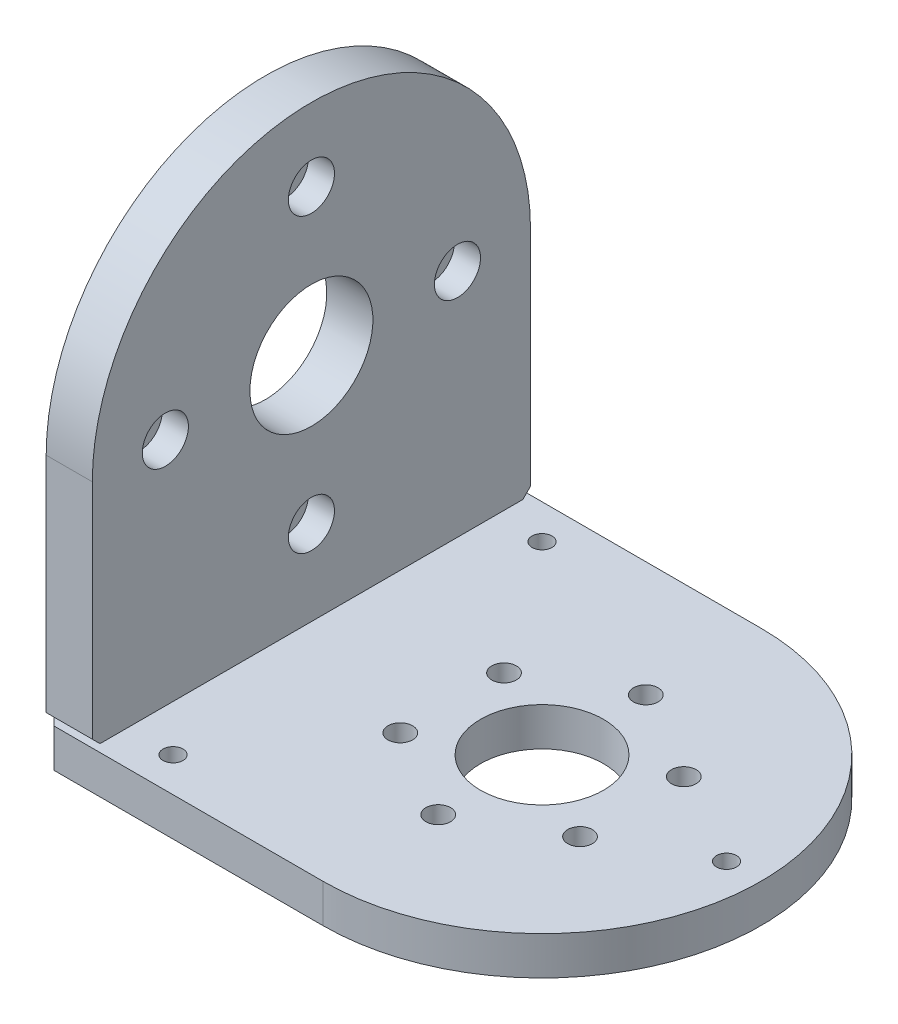
SolidWorks part; units mm, degrees
material "5052-H32"
ref_plane "前视基准面" through (0, 0, 0) normal (0, 0, 1) x (1, 0, 0)
ref_plane "上视基准面" through (0, 0, 0) normal (0, 1, 0) x (1, 0, 0)
ref_plane "右视基准面" through (0, 0, 0) normal (1, 0, 0) x (0, 0, -1)
other "Configuration Table"
sketch "草图1" plane through (0, 0, 0) normal (0, 1, 0) x (1, 0, 0)
  line L1 (-33, 28.5) -> (33, 28.5)
  line L2 (-33, 28.5) -> (-33, -28.5)
  line L3 (-33, -28.5) -> (33, -28.5)
  line L4 (33, 28.5) -> (33, -28.5)
  line L5 (-33, 28.5) -> (33, -28.5) construction
  line L6 (-33, -28.5) -> (33, 28.5) construction
  point P0 (0, 0)
  dimension "D1" = 66
  dimension "D2" = 57
extrude "凸台-拉伸1" add sketch "草图1" along normal blind 5
sketch "草图12" plane through (-33, 0, 0) normal (-1, 0, 0) x (0, 0, 1)
  line L0 (28.5, 5) -> (28.5, 0) construction
  line L1 (-28.5, 5) -> (28.5, 5)
  line L2 (-28.5, 5) -> (-28.5, 65)
  line L3 (-28.5, 65) -> (28.5, 65)
  line L4 (28.5, 5) -> (28.5, 65)
  dimension "D1" = 60
extrude "凸台-拉伸2" add sketch "草图12" against normal blind 6 separate body
sketch "草图13" plane through (0, 5, 0) normal (0, 1, 0) x (1, 0, 0)
  line L0 (33, -28.5) -> (33, 28.5) construction
  line L1 (33, 28.5) -> (-33, 28.5) construction
  line L2 (-33, -28.5) -> (33, -28.5) construction
  line L3 (3, -28.5) -> (33, -28.5)
  line L4 (33, -28.5) -> (33, 28.5)
  line L5 (33, 28.5) -> (3, 28.5)
  circle A0 centre (3, 0) radius 8
  arc A1 (3, -28.5) -> (3, 28.5) centre (3, 0) ccw
  dimension "D1" = 30
  dimension "D2" = 16
extrude "切除-拉伸2" cut sketch "草图13" against normal blind 6
sketch "草图14" plane through (-33, 0, 0) normal (-1, 0, 0) x (0, 0, 1)
  line L0 (28.5, 65) -> (-28.5, 65) construction
  circle A0 centre (0, 35) radius 8
  dimension "D1" = 16
  dimension "D2" = 30
extrude "切除-拉伸3" cut sketch "草图14" against normal blind 6
sketch "草图15" plane through (-33, 0, 0) normal (-1, 0, 0) x (0, 0, 1)
  line L0 (28.5, 5) -> (28.5, 65) construction
  line L1 (28.5, 65) -> (-28.5, 65) construction
  line L2 (-28.5, 65) -> (-28.5, 5) construction
  line L3 (28.5, 35) -> (28.5, 65)
  line L4 (28.5, 65) -> (-28.5, 65)
  line L5 (-28.5, 65) -> (-28.5, 35)
  arc A0 (28.5, 35) -> (-28.5, 35) centre (0, 35) ccw
  circle A1 centre (0, 35) radius 8 construction
  dimension "D1" = 28.5
extrude "切除-拉伸4" cut sketch "草图15" against normal blind 10 contours A0 L5 L4 L3
sketch "草图16" plane through (0, 0, 0) normal (0, -1, 0) x (1, 0, 0)
  circle A0 centre (3, 0) radius 13.5 construction
  circle A1 centre (3, 13.5) radius 1.6
  circle A2 centre (14.6913, 6.75) radius 1.6
  circle A3 centre (14.6913, -6.75) radius 1.6
  circle A4 centre (3, -13.5) radius 1.6
  circle A5 centre (-8.6913, -6.75) radius 1.6
  circle A6 centre (-8.6913, 6.75) radius 1.6
  point P18 (3, 0)
  dimension "D1" = 27
  dimension "D2" = 3.2
  dimension "D3" = 6
extrude "切除-拉伸5" cut sketch "草图16" against normal blind 10
sketch "草图18" plane through (0, 0, 0) normal (0, -1, 0) x (1, 0, 0)
  line L0 (34.925, 0) -> (-34.925, 0) construction
  line L1 (-33, -28.5) -> (-33, 28.5) construction
  circle A0 centre (-30, -22) radius 1.7
  circle A1 centre (-30, 22) radius 1.7
  circle A2 centre (-30, 0) radius 1.7
  point P11 (-33, 0)
  dimension "D1" = 3
  dimension "D3" = 3.4
  dimension "D4" = 3.4
  dimension "D2" = 44
extrude "切除-拉伸6" cut sketch "草图18" against normal up to surface (5 mm away) up to face at (3, 5, 15.1)
chamfer "倒角1" distance 1 angle 45 2 edges at (-33, 2.5, 28.5) (-33, 2.5, -28.5)
sketch "草图22" plane through (-27, 0, 0) normal (1, 0, 0) x (0, 0, -1)
  circle A0 centre (0, 35) radius 19 construction
  circle A1 centre (0, 54) radius 1.6
  circle A2 centre (-19, 35) radius 1.6
  circle A3 centre (19, 35) radius 1.6
  circle A4 centre (0, 16) radius 1.6
  dimension "D1" = 38
  dimension "D2" = 3.2
extrude "切除-拉伸7" cut sketch "草图22" against normal up to next (6 mm away) and the other way through all
hole_wizard "M3 六角圆柱头螺钉的柱形沉头孔1" positions "3D草图2" profile "草图23" counterbore size "M3" standard "GB"
sketch3d "3D草图2"
  circle A0 centre (-33, 54, 0) radius 1.6 construction
  circle A1 centre (-33, 35, -19) radius 1.6 construction
  circle A2 centre (-33, 35, 19) radius 1.6 construction
  circle A3 centre (-33, 16, 0) radius 1.6 construction
  point P0 (-27, 35, -19)
  point P2 (-27, 54, 0)
  point P4 (-27, 35, 19)
  point P6 (-27, 16, 0)
  point P12 (-34.6, 54, 0)
  point P16 (-34.6, 35, -19)
  point P20 (-34.6, 35, 19)
  point P23 (-34.6, 16, 0)
sketch "草图23" plane through (-27, 35, -19) normal (0, 1, 0) x (0, 0, -1)
  line L0 (0, 0) -> (0, 13.4215)
  line L1 (0, 13.4215) -> (1.7, 12.4)
  line L2 (1.7, 12.4) -> (1.7, 3.4)
  line L3 (1.7, 3.4) -> (3, 3.4)
  line L4 (3, 3.4) -> (3, 0)
  line L5 (3, 0) -> (0, 0)
  line L10 (0, 13.4215) -> (-1.7, 12.4) construction
  line L11 (0, -6.35) -> (0, 107.95) construction
  dimension "孔直径" = 3.4
  dimension "孔深度" = 12.4
  dimension "柱形沉头孔直径" = 6
  dimension "柱形沉头孔深度" = 3.4
  dimension "导头角度" = 118
hole_wizard "M3 螺纹孔1" positions "草图24" profile "草图25" tap size "M3" standard "GB"
sketch "草图24" plane through (0, 5, 0) normal (0, -1, 0) x (-1, 0, 0)
  circle A0 centre (30, 0) radius 1.7 construction
  circle A2 centre (30, -22) radius 1.7 construction
  circle A3 centre (30, 22) radius 1.7 construction
  point P0 (30, 22)
  point P3 (30, 0)
  point P5 (30, -22)
  point P13 (37.1599, -20.6304)
sketch "草图25" plane through (-30, 5, -22) normal (1, 0, 0) x (0, 0, -1)
  line L0 (0, 0) -> (0, 7.7511)
  line L1 (0, 7.7511) -> (1.25, 7)
  line L2 (1.25, 7) -> (1.25, 0)
  line L5 (1.25, 0) -> (0, 0)
  line L10 (0, 7.7511) -> (-1.25, 7) construction
  line L11 (0, -6.35) -> (0, 107.95) construction
  dimension "螺纹孔钻头直径" = 2.5
  dimension "螺纹孔钻头深度" = 7
  dimension "导头角度" = 118
cosmetic thread "孔螺蚊线1" parameters "D1"=5, "D2"=3
cosmetic thread "孔螺蚊线2" parameters "D1"=5, "D2"=3
cosmetic thread "孔螺蚊线3" parameters "D1"=5, "D2"=3
sketch "草图26" plane through (0, 5, 0) normal (0, 1, 0) x (1, 0, 0)
  line L0 (-34.925, 0) -> (34.925, 0) construction
  line L1 (-33, 20.6252) -> (-33, -20.6252) construction
  circle A0 centre (-21, 24) radius 1.3
  circle A1 centre (-21, -24) radius 1.3
  circle A2 centre (27, 0) radius 1.3
  circle A3 centre (3, 0) radius 8 construction
  point P10 (22.095, 4.3262)
  dimension "D1" = 2.6
  dimension "D3" = 48
  dimension "D4" = 24
  dimension "D2" = 12
extrude "切除-拉伸8" cut sketch "草图26" against normal through all
chamfer "倒角2" distance 1 angle 45 2 edges at (-30, 5, -28.5) (-30, 5, 28.5)
